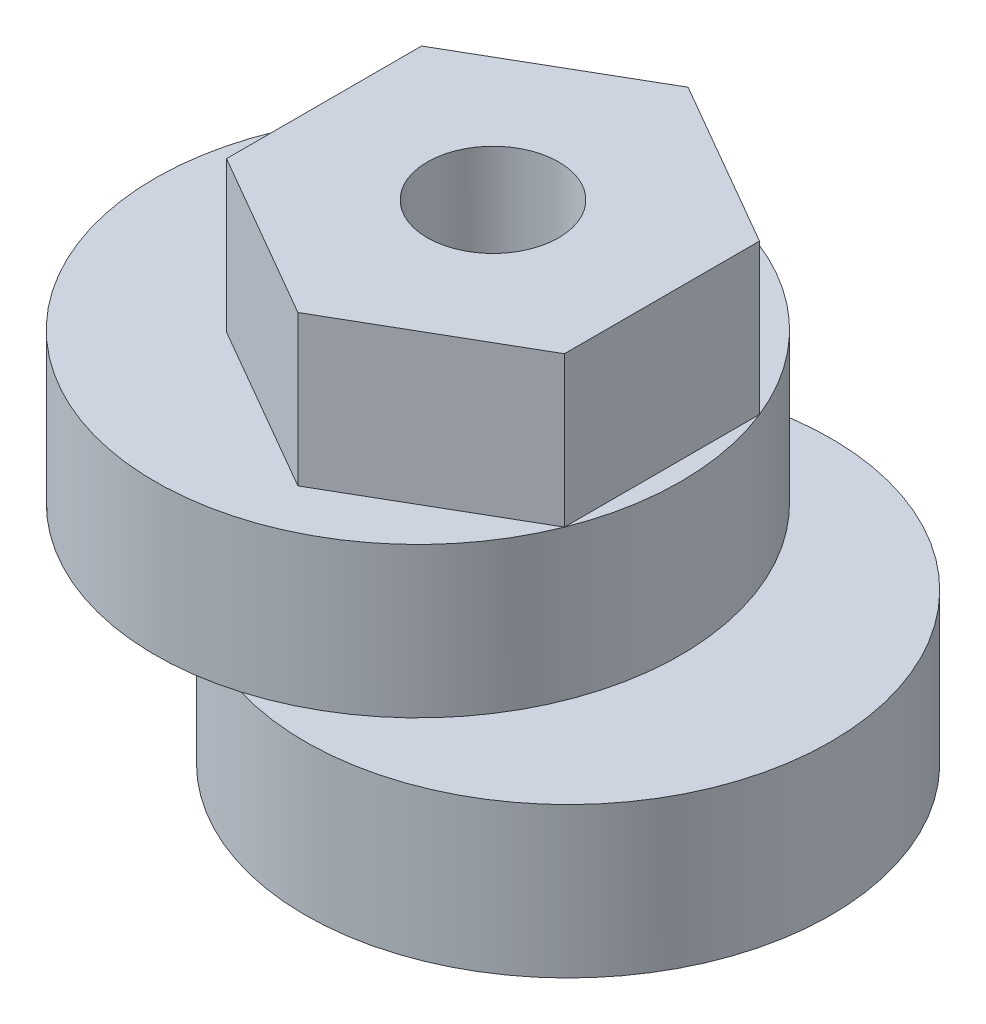
SolidWorks part; units mm, degrees
ref_plane "Front Plane" through (0, 0, 0) normal (0, 0, 1) x (1, 0, 0)
ref_plane "Top Plane" through (0, 0, 0) normal (0, 1, 0) x (1, 0, 0)
ref_plane "Right Plane" through (0, 0, 0) normal (1, 0, 0) x (0, 0, -1)
sketch "Sketch1" plane through (0, 0, 0) normal (0, 1, 0) x (1, 0, 0)
  circle A0 centre (0, 0) radius 5
  dimension "D1" = 10
extrude "Boss-Extrude1" add sketch "Sketch1" along normal blind 2
sketch "Sketch2" plane through (0, 2, 0) normal (0, 1, 0) x (1, 0, 0)
  circle A0 centre (2, 0) radius 7
  circle A1 centre (0, 0) radius 5 construction
  point P5 (0, 0)
  dimension "D1" = 14
  dimension "D2" = 2
extrude "Boss-Extrude2" add sketch "Sketch2" along normal blind 4
sketch "Sketch4" plane through (0, 6, 0) normal (0, 1, 0) x (1, 0, 0)
  circle A0 centre (-2, 0) radius 7
  point P2 (-8.3636, 0)
  point P4 (-1.6517, -1.1278)
  point P5 (0, 0)
  dimension "D1" = 14
  dimension "D2" = 2
extrude "Boss-Extrude4" add sketch "Sketch4" along normal blind 4
sketch "Sketch5" plane through (0, 0, 0) normal (0, -1, 0) x (1, 0, 0)
  circle A0 centre (0, 0) radius 1.75
  dimension "D1" = 3.5
extrude "Cut-Extrude1" cut sketch "Sketch5" against normal through all
sketch "Sketch6" plane through (0, 10, 0) normal (0, 1, 0) x (1, 0, 0)
  line L1 (-4.5, 2.5981) -> (-4.5, -2.5981)
  line L2 (-4.5, -2.5981) -> (0, -5.1962)
  line L3 (0, -5.1962) -> (4.5, -2.5981)
  line L4 (4.5, -2.5981) -> (4.5, 2.5981)
  line L5 (4.5, 2.5981) -> (0, 5.1962)
  line L6 (0, 5.1962) -> (-4.5, 2.5981)
  circle A0 centre (0, 0) radius 4.5 construction
  circle A1 centre (-2, 0) radius 7 construction
  circle A2 centre (0, 0) radius 1.75 construction
  circle A3 centre (0, 0) radius 1.75
extrude "Boss-Extrude5" add sketch "Sketch6" along normal blind 4
